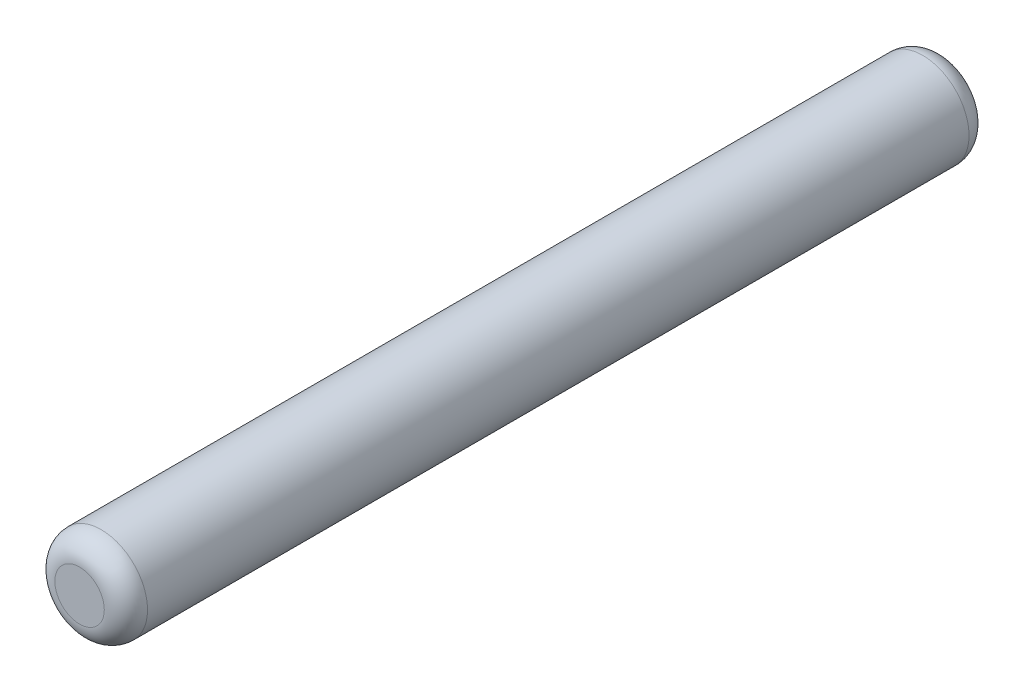
SolidWorks part; units mm, degrees
ref_plane "Front" through (0, 0, 0) normal (0, 0, 1) x (1, 0, 0)
ref_plane "Top" through (0, 0, 0) normal (0, 1, 0) x (1, 0, 0)
ref_plane "Right" through (0, 0, 0) normal (1, 0, 0) x (0, 0, -1)
sketch "Sketch1" plane through (0, 0, 0) normal (0, 0, 1) x (1, 0, 0)
  circle A0 centre (0, 0) radius 0.75
  dimension "D1" = 1.5
extrude "Boss-Extrude1" add sketch "Sketch1" along normal mid plane 14
fillet "Fillet1" radius 0.35 2 edges at (0.75, 0, -7) (0.75, 0, 7)
